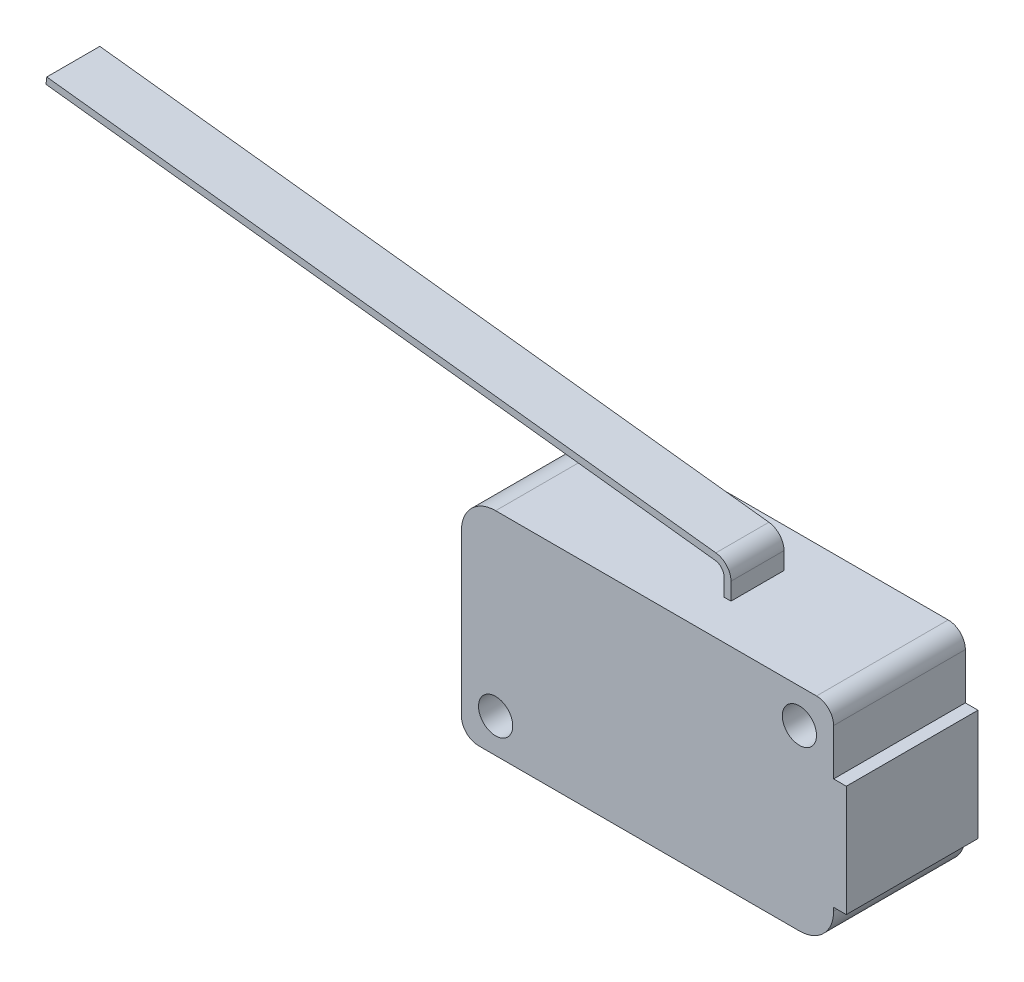
SolidWorks part; units mm, degrees
ref_plane "Front Plane" through (0, 0, 0) normal (0, 0, 1) x (1, 0, 0)
ref_plane "Top Plane" through (0, 0, 0) normal (0, 1, 0) x (1, 0, 0)
ref_plane "Right Plane" through (0, 0, 0) normal (1, 0, 0) x (0, 0, -1)
sketch "Sketch1" plane through (0, 0, 0) normal (0, 0, 1) x (1, 0, 0)
  line L0 (-50.8, 8.3058) -> (-50.8, 0) construction
  line L1 (0, 8.3058) -> (-50.8, 8.3058) construction
  line L2 (-14.5542, 0) -> (9.271, 0)
  line L3 (0, 1.2818) -> (0, 0)
  line L4 (-1.1237, 2.5433) -> (-50.8, 8.3058)
  line L5 (10.541, -1.27) -> (10.541, -4.699)
  line L6 (0, 8.3058) -> (0, 2.413) construction
  line L7 (8.001, -15.748) -> (-15.8242, -15.748)
  line L8 (-17.0942, -14.478) -> (-17.0942, -2.54)
  line L9 (11.4808, -4.699) -> (11.4808, -12.954)
  line L10 (11.4808, -4.699) -> (10.541, -4.699)
  line L11 (11.4808, -12.954) -> (10.541, -12.954)
  line L12 (10.541, -12.954) -> (10.541, -13.208)
  arc A0 (10.541, -13.208) -> (8.001, -15.748) centre (8.001, -13.208) cw
  arc A1 (10.541, -1.27) -> (9.271, 0) centre (9.271, -1.27) ccw
  arc A2 (-17.0942, -14.478) -> (-15.8242, -15.748) centre (-15.8242, -14.478) ccw
  arc A3 (-17.0942, -2.54) -> (-14.5542, 0) centre (-14.5542, -2.54) cw
  arc A4 (-1.1237, 2.5433) -> (0, 1.2818) centre (-1.27, 1.2818) cw
  point P16 (10.541, -15.748)
  point P19 (10.541, 0)
  point P22 (-17.0942, -15.748)
  point P28 (-3.9116, -15.748)
  dimension "D10" = 2.54
  dimension "D11" = 1.27
  dimension "D12" = 1.27
  dimension "D1" = 8.3058
  dimension "D2" = 50.8
  dimension "D3" = 2.413
  dimension "D4" = 10.541
  dimension "D5" = 15.748
  dimension "D6" = 27.6352
  dimension "D7" = 28.575
  dimension "D8" = 4.699
  dimension "D9" = 2.794
extrude "Extrude-Thin1" add sketch "Sketch1" against normal blind 1.9685 thin contours L4 A4 L3
sketch "Sketch2" plane through (0, 0, 0) normal (0, 0, 1) x (1, 0, 0)
  line L0 (-50.8, 8.3058) -> (-50.8, 0) construction
  line L1 (0, 8.3058) -> (-50.8, 8.3058) construction
  line L2 (-14.5542, 0) -> (9.271, 0)
  line L3 (0, 1.2818) -> (0, 0)
  line L4 (-1.1237, 2.5433) -> (-50.8, 8.3058)
  line L5 (10.541, -1.27) -> (10.541, -4.699)
  line L6 (0, 8.3058) -> (0, 2.413) construction
  line L7 (8.001, -15.748) -> (-15.8242, -15.748)
  line L8 (-17.0942, -14.478) -> (-17.0942, -2.54)
  line L9 (11.4808, -4.699) -> (11.4808, -12.954)
  line L10 (11.4808, -4.699) -> (10.541, -4.699)
  line L11 (11.4808, -12.954) -> (10.541, -12.954)
  line L12 (10.541, -12.954) -> (10.541, -13.208)
  line L13 (9.271, -2.54) -> (10.541, -2.54) construction
  line L14 (8.001, -1.27) -> (8.001, 0) construction
  line L15 (-14.5542, -14.478) -> (-14.5542, -15.748) construction
  line L16 (-15.8242, -13.208) -> (-17.0942, -13.208) construction
  arc A0 (10.541, -13.208) -> (8.001, -15.748) centre (8.001, -13.208) cw
  arc A1 (10.541, -1.27) -> (9.271, 0) centre (9.271, -1.27) ccw
  arc A2 (-17.0942, -14.478) -> (-15.8242, -15.748) centre (-15.8242, -14.478) ccw
  arc A3 (-17.0942, -2.54) -> (-14.5542, 0) centre (-14.5542, -2.54) cw
  arc A4 (-1.1237, 2.5433) -> (0, 1.2818) centre (-1.27, 1.2818) cw
  circle A5 centre (8.001, -2.54) radius 1.27
  circle A6 centre (-14.5542, -13.208) radius 1.27
  point P16 (10.541, -15.748)
  point P19 (10.541, 0)
  point P22 (-17.0942, -15.748)
  point P28 (-3.9116, -15.748)
  dimension "D10" = 2.54
  dimension "D11" = 1.27
  dimension "D12" = 1.27
  dimension "D15" = 2.54
  dimension "D1" = 8.3058
  dimension "D2" = 50.8
  dimension "D3" = 2.413
  dimension "D4" = 10.541
  dimension "D5" = 15.748
  dimension "D6" = 27.6352
  dimension "D7" = 28.575
  dimension "D8" = 4.699
  dimension "D9" = 2.794
  dimension "D13" = 1.27
extrude "Boss-Extrude1" add sketch "Sketch2" against normal blind 4.8895 contours A3 L8 A2 L7 A0 L12 L11 L9 L10 L5 A1 L2
mirror "Mirror1" of "Extrude-Thin1", "Boss-Extrude1"
